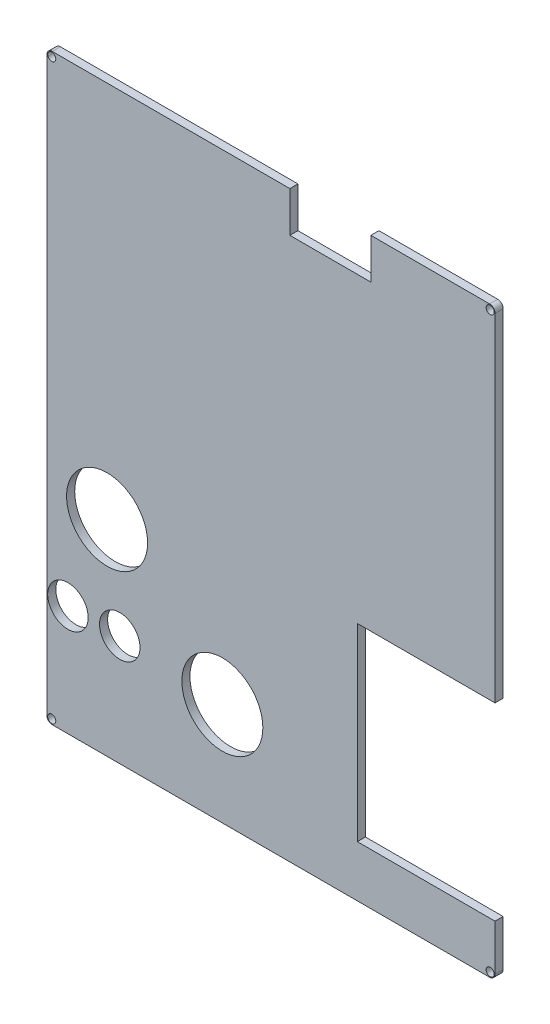
SolidWorks part; units mm, degrees
ref_plane "Plan de face" through (0, 0, 0) normal (0, 0, 1) x (1, 0, 0)
ref_plane "Plan de dessus" through (0, 0, 0) normal (0, 1, 0) x (1, 0, 0)
ref_plane "Plan de droite" through (0, 0, 0) normal (1, 0, 0) x (0, 0, -1)
sketch "Esquisse1" plane through (0, 0, 0) normal (0, 0, 1) x (1, 0, 0)
  line L1 (-166.2693, 130.411) -> (-6.2693, 130.411)
  line L2 (-166.2693, 130.411) -> (-166.2693, -79.589)
  line L3 (-166.2693, -79.589) -> (-6.2693, -79.589)
  line L4 (-6.2693, 130.411) -> (-6.2693, -79.589)
  dimension "D1" = 210
  dimension "D2" = 160
extrude "Boss.-Extru.1" add sketch "Esquisse1" along normal blind 3 contours L2 L1 L4 L3
fillet "Congé6" radius 2 1 edges at (-166.2693, 130.411, 1.5)
sketch "Esquisse4" plane through (0, 0, 3) normal (0, 0, 1) x (1, 0, 0)
  line L0 (-164.2693, 130.411) -> (-6.2693, 130.411) construction
  line L1 (-166.2693, 128.411) -> (-166.2693, -79.589) construction
  circle A0 centre (-164.4693, 128.611) radius 1.5
  dimension "D3" = 3
  dimension "D1" = 1.8
  dimension "D2" = 1.8
extrude "Enlèv. mat.-Extru.3" cut sketch "Esquisse4" against normal blind 4
sketch "Esquisse6" plane through (0, 0, 3) normal (0, 0, 1) x (1, 0, 0)
  line L0 (-6.2693, 128.411) -> (-6.2693, -77.589) construction
  line L1 (-51.2693, 3.411) -> (-6.2693, 3.411)
  line L2 (-51.2693, 3.411) -> (-51.2693, -66.589)
  line L3 (-51.2693, -66.589) -> (-6.2693, -66.589)
  line L4 (-6.2693, 3.411) -> (-6.2693, -66.589)
  line L5 (-166.2693, -79.589) -> (-8.2693, -79.589) construction
  dimension "D1" = 13
  dimension "D2" = 45
  dimension "D3" = 70
extrude "Enlèv. mat.-Extru.5" cut sketch "Esquisse6" against normal blind 4 contours L2 L1 L4 L3
sketch "Esquisse7" plane through (0, 0, 3) normal (0, 0, 1) x (1, 0, 0)
  line L0 (-6.2693, -66.589) -> (-6.2693, -79.589) construction
  line L1 (-166.2693, -79.589) -> (-6.2693, -79.589) construction
  circle A0 centre (-101.2693, -47.589) radius 15
  dimension "D1" = 95
  dimension "D2" = 30
  dimension "D3" = 32
extrude "Enlèv. mat.-Extru.6" cut sketch "Esquisse7" against normal blind 856
sketch "Esquisse8" plane through (0, 0, 3) normal (0, 0, 1) x (1, 0, 0)
  line L0 (-166.2693, -79.589) -> (-6.2693, -79.589) construction
  circle A0 centre (-143.9661, -9.589) radius 15
  dimension "D2" = 30
  dimension "D1" = 70
extrude "Enlèv. mat.-Extru.7" cut sketch "Esquisse8" against normal blind 856
sketch "Esquisse9" plane through (0, 0, 3) normal (0, 0, 1) x (1, 0, 0)
  line L0 (-166.2693, -79.589) -> (-6.2693, -79.589) construction
  line L1 (-166.2693, 128.411) -> (-166.2693, -79.589) construction
  circle A0 centre (-139.2693, -44.589) radius 7.5
  dimension "D1" = 15
  dimension "D2" = 35
  dimension "D3" = 27
extrude "Enlèv. mat.-Extru.8" cut sketch "Esquisse9" against normal blind 856
sketch "Esquisse10" plane through (0, 0, 3) normal (0, 0, 1) x (1, 0, 0)
  line L0 (-166.2693, -79.589) -> (-6.2693, -79.589) construction
  line L1 (-166.2693, 128.411) -> (-166.2693, -79.589) construction
  circle A0 centre (-158.4693, -44.589) radius 7.5
  dimension "D1" = 35
  dimension "D2" = 7.8
extrude "Enlèv. mat.-Extru.13" cut sketch "Esquisse10" against normal blind 856
sketch "Esquisse12" plane through (0, 0, 3) normal (0, 0, 1) x (1, 0, 0)
  line L0 (-6.2693, 130.411) -> (-6.2693, 3.411) construction
  line L1 (-76.2693, 115.411) -> (-46.2693, 115.411)
  line L2 (-76.2693, 115.411) -> (-76.2693, 130.411)
  line L3 (-76.2693, 130.411) -> (-46.2693, 130.411)
  line L4 (-46.2693, 115.411) -> (-46.2693, 130.411)
  line L5 (-164.2693, 130.411) -> (-6.2693, 130.411) construction
  dimension "D1" = 40
  dimension "D2" = 70
  dimension "D3" = 15
  dimension "D4" = 0
extrude "Enlèv. mat.-Extru.14" cut sketch "Esquisse12" against normal blind 856
sketch "Esquisse13" plane through (0, -79.589, 0) normal (0, -1, 0) x (1, 0, 0)
  line L2 (-166.2693, 0) -> (-6.2693, 0)
  line L3 (-166.2693, 0) -> (-166.2693, 3)
  line L4 (-166.2693, 3) -> (-6.2693, 3)
  line L5 (-6.2693, 0) -> (-6.2693, 3)
extrude "Boss.-Extru.2" add sketch "Esquisse13" along normal blind 3
sketch "Esquisse14" plane through (-6.2693, 0, 0) normal (1, 0, 0) x (0, 0, -1)
  line L1 (-3, 130.411) -> (0, 130.411)
  line L2 (-3, 130.411) -> (-3, -82.589)
  line L3 (-3, -82.589) -> (0, -82.589)
  line L4 (0, 130.411) -> (0, -82.589)
extrude "Boss.-Extru.3" add sketch "Esquisse14" along normal blind 3
sketch "Esquisse15" plane through (-3.2693, 0, 0) normal (1, 0, 0) x (0, 0, -1)
  line L0 (-3, 130.411) -> (-3, -82.589) construction
  line L1 (-3, 3.411) -> (0, 3.411)
  line L2 (-3, 3.411) -> (-3, -66.589)
  line L3 (-3, -66.589) -> (0, -66.589)
  line L4 (0, 3.411) -> (0, -66.589)
  line L5 (0, -82.589) -> (0, 130.411) construction
  dimension "D1" = 0
  dimension "D2" = 0
extrude "Enlèv. mat.-Extru.15" cut sketch "Esquisse15" against normal blind 4
sketch "Esquisse18" plane through (-3.2693, 0, 0) normal (1, 0, 0) x (0, 0, -1)
  line L1 (-3, 130.411) -> (0, 130.411)
  line L2 (-3, 130.411) -> (-3, -82.589)
  line L3 (-3, -82.589) -> (0, -82.589)
  line L4 (0, 130.411) -> (0, -82.589)
extrude "Boss.-Extru.4" add sketch "Esquisse18" along normal blind 3
sketch "Esquisse19" plane through (0, -82.589, 0) normal (0, -1, 0) x (-1, 0, 0)
  line L1 (166.2693, -3) -> (0.2693, -3)
  line L2 (166.2693, -3) -> (166.2693, 0)
  line L3 (166.2693, 0) -> (0.2693, 0)
  line L4 (0.2693, -3) -> (0.2693, 0)
extrude "Boss.-Extru.5" add sketch "Esquisse19" along normal blind 3
sketch "Esquisse20" plane through (-0.2693, 0, 0) normal (1, 0, 0) x (0, 0, -1)
  line L1 (-3, 130.411) -> (-3, -85.589) construction
  line L2 (-3, -66.589) -> (0, -66.589)
  line L3 (-3, -66.589) -> (-3, 3.411)
  line L4 (-3, 3.411) -> (0, 3.411)
  line L5 (0, -66.589) -> (0, 3.411)
  line L6 (0, -85.589) -> (0, 130.411) construction
  line L7 (-3, -66.589) -> (0, -66.589) construction
  line L8 (0, 3.411) -> (-3, 3.411) construction
  dimension "D1" = 0
  dimension "D2" = 0
extrude "Enlèv. mat.-Extru.16" cut sketch "Esquisse20" against normal blind 3
sketch "Esquisse21" plane through (0, 0, 3) normal (0, 0, 1) x (1, 0, 0)
  line L0 (-46.2693, 130.411) -> (-0.2693, 130.411) construction
  line L1 (-0.2693, 130.411) -> (-0.2693, 3.411) construction
  circle A0 centre (-2.0693, 128.611) radius 1.5
  dimension "D1" = 1.8
  dimension "D2" = 1.8
extrude "Enlèv. mat.-Extru.17" cut sketch "Esquisse21" against normal blind 3
sketch "Esquisse22" plane through (0, 0, 3) normal (0, 0, 1) x (1, 0, 0)
  line L0 (-0.2693, -66.589) -> (-0.2693, -85.589) construction
  line L1 (-0.2693, -85.589) -> (-166.2693, -85.589) construction
  circle A0 centre (-2.0693, -83.789) radius 1.5
  dimension "D1" = 1.8
  dimension "D2" = 1.8
extrude "Enlèv. mat.-Extru.18" cut sketch "Esquisse22" against normal blind 3
sketch "Esquisse23" plane through (0, 0, 3) normal (0, 0, 1) x (1, 0, 0)
  line L0 (-0.2693, -85.589) -> (-166.2693, -85.589) construction
  line L1 (-166.2693, 128.411) -> (-166.2693, -85.589) construction
  circle A0 centre (-164.4693, -83.789) radius 1.5
  dimension "D1" = 1.8
  dimension "D2" = 1.8
extrude "Enlèv. mat.-Extru.19" cut sketch "Esquisse23" against normal blind 3
fillet "Congé7" radius 2 1 edges at (-0.2693, -85.589, 1.5)
fillet "Congé8" radius 2 1 edges at (-0.2693, 130.411, 1.5)
fillet "Congé9" radius 2 1 edges at (-166.2693, -85.589, 1.5)
